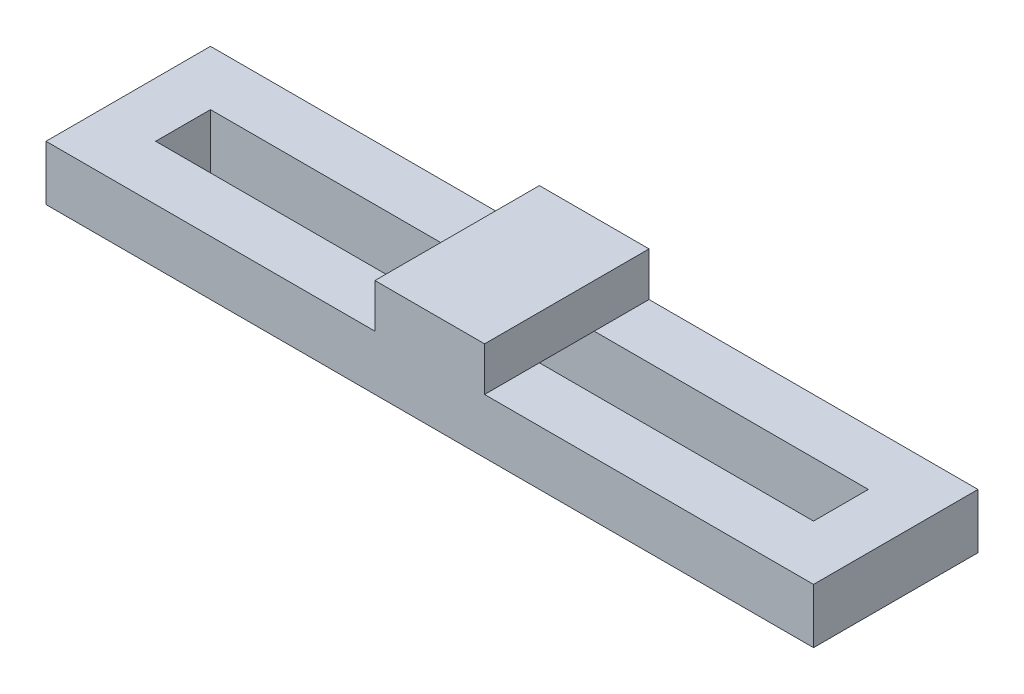
SolidWorks part; units mm, degrees
ref_plane "Front Plane" through (0, 0, 0) normal (0, 0, 1) x (1, 0, 0)
ref_plane "Top Plane" through (0, 0, 0) normal (0, 1, 0) x (1, 0, 0)
ref_plane "Right Plane" through (0, 0, 0) normal (1, 0, 0) x (0, 0, -1)
sketch "Sketch2" plane through (0, 0, 0) normal (0, 1, 0) x (1, 0, 0)
  line L1 (-35, -7.5) -> (35, -7.5)
  line L2 (-35, -7.5) -> (-35, 7.5)
  line L3 (-35, 7.5) -> (35, 7.5)
  line L4 (35, -7.5) -> (35, 7.5)
  line L5 (-35, -7.5) -> (35, 7.5) construction
  line L6 (-35, 7.5) -> (35, -7.5) construction
  line L7 (30, -2.5) -> (-30, -2.5)
  line L8 (30, -2.5) -> (30, 2.5)
  line L9 (30, 2.5) -> (-30, 2.5)
  line L10 (-30, -2.5) -> (-30, 2.5)
  line L11 (30, -2.5) -> (-30, 2.5) construction
  line L12 (30, 2.5) -> (-30, -2.5) construction
  point P0 (0, 0)
  point P6 (0, 0)
  dimension "D1" = 70
  dimension "D2" = 15
  dimension "D3" = 60
  dimension "D4" = 5
extrude "Boss-Extrude3" add sketch "Sketch2" along normal blind 5
sketch "Sketch3" plane through (0, 5, 0) normal (0, 1, 0) x (1, 0, 0)
  line L0 (35, 7.5) -> (-35, 7.5) construction
  line L1 (-5, -7.5) -> (5, -7.5)
  line L2 (-5, -7.5) -> (-5, 7.5)
  line L3 (-5, 7.5) -> (5, 7.5)
  line L4 (5, -7.5) -> (5, 7.5)
  line L5 (-5, -7.5) -> (5, 7.5) construction
  line L6 (-5, 7.5) -> (5, -7.5) construction
  point P0 (0, 0)
  dimension "D1" = 10
extrude "Boss-Extrude4" add sketch "Sketch3" along normal blind 4
